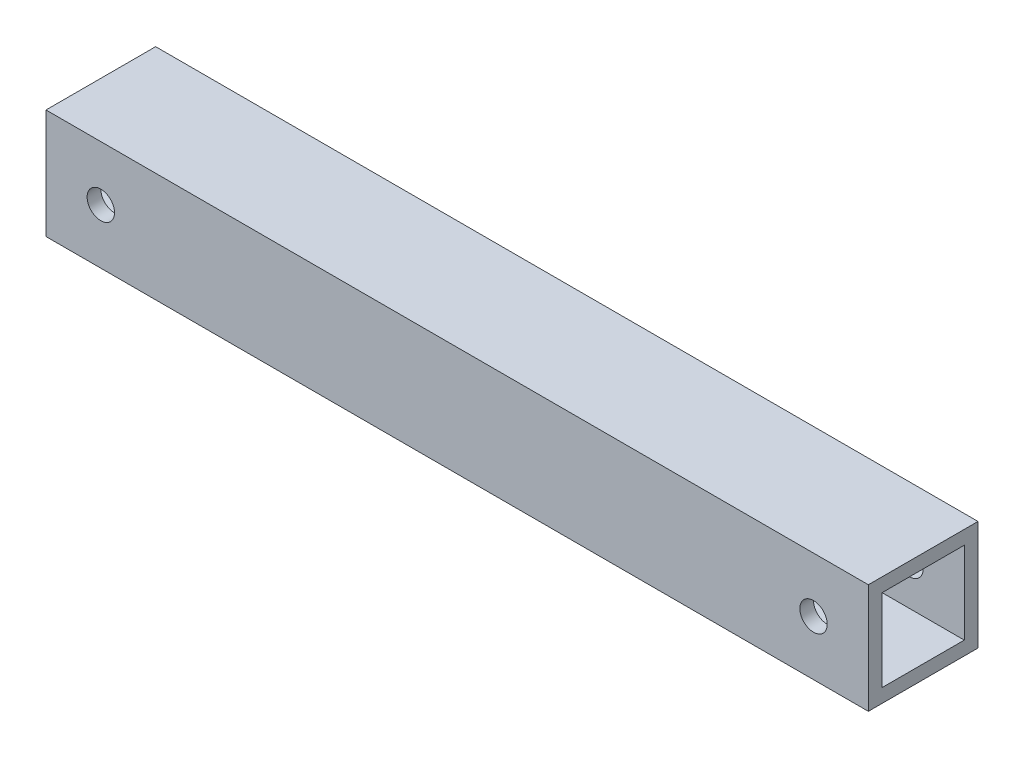
SolidWorks part; units mm, degrees
ref_plane "Front Plane" through (0, 0, 0) normal (0, 0, 1) x (1, 0, 0)
ref_plane "Top Plane" through (0, 0, 0) normal (0, 1, 0) x (1, 0, 0)
ref_plane "Right Plane" through (0, 0, 0) normal (1, 0, 0) x (0, 0, -1)
sketch "Sketch1" plane through (0, 0, 0) normal (0, 0, 1) x (1, 0, 0)
  line L1 (-95.25, -12.7) -> (95.25, -12.7)
  line L2 (-95.25, -12.7) -> (-95.25, 12.7)
  line L3 (-95.25, 12.7) -> (95.25, 12.7)
  line L4 (95.25, -12.7) -> (95.25, 12.7)
  line L5 (-95.25, -12.7) -> (95.25, 12.7) construction
  line L6 (-95.25, 12.7) -> (95.25, -12.7) construction
  point P0 (0, 0)
extrude "Boss-Extrude1" add sketch "Sketch1" along normal blind 25.4
sketch "Sketch2" plane through (95.25, 0, 0) normal (1, 0, 0) x (0, 0, -1)
  line L0 (-12.7, 12.7) -> (-12.7, -12.7)
  line L1 (-25.4, 12.7) -> (0, 12.7) construction
  line L2 (-25.4, -12.7) -> (0, -12.7) construction
  line L3 (-3.175, 9.5204) -> (-3.175, 12.7)
  line L4 (-22.225, -9.5204) -> (-3.175, -9.5204)
  line L5 (-22.225, -9.5204) -> (-22.225, 9.5204)
  line L6 (-22.225, 9.5204) -> (-3.175, 9.5204)
  line L7 (-3.175, -9.5204) -> (-3.175, 9.5204)
  line L8 (-22.225, -9.5204) -> (-3.175, 9.5204) construction
  line L9 (-22.225, 9.5204) -> (-3.175, -9.5204) construction
  line L10 (-3.175, 9.5204) -> (0, 9.5204)
  line L11 (0, -12.7) -> (0, 12.7) construction
  point P6 (-12.7, 0)
extrude "Cut-Extrude1" cut sketch "Sketch2" against normal blind 508 contours L6 L5 L4 L0 | L4 L7 L6 L0
sketch "Sketch4" plane through (0, 0, 25.4) normal (0, 0, 1) x (1, 0, 0)
  line L0 (-95.25, 0) -> (-82.55, 0)
  line L1 (-95.25, 12.7) -> (-95.25, -12.7) construction
  line L2 (95.25, 0) -> (82.55, 0)
  line L4 (95.25, -12.7) -> (95.25, 12.7) construction
  circle A0 centre (-82.55, 0) radius 3.175
  circle A1 centre (82.55, 0) radius 3.175
  point P11 (-38.2202, 0)
  point P12 (39.7696, 0)
extrude "Cut-Extrude3" cut sketch "Sketch4" against normal blind 508
